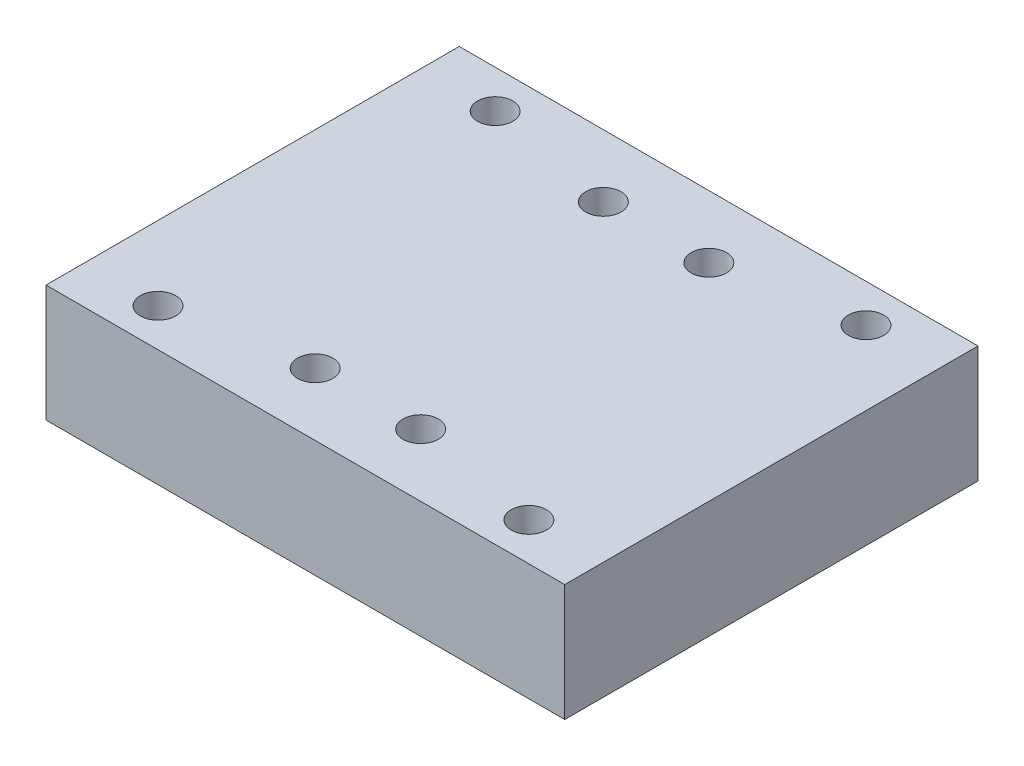
SolidWorks part; units mm, degrees
ref_plane "Front Plane" through (0, 0, 0) normal (0, 0, 1) x (1, 0, 0)
ref_plane "Top Plane" through (0, 0, 0) normal (0, 1, 0) x (1, 0, 0)
ref_plane "Right Plane" through (0, 0, 0) normal (1, 0, 0) x (0, 0, -1)
sketch "Sketch1" plane through (0, 0, 0) normal (0, 1, 0) x (1, 0, 0)
  line L1 (-47.7, -38) -> (47.7, -38)
  line L2 (-47.7, -38) -> (-47.7, 38)
  line L3 (-47.7, 38) -> (47.7, 38)
  line L4 (47.7, -38) -> (47.7, 38)
  line L5 (-47.7, -38) -> (47.7, 38) construction
  line L6 (-47.7, 38) -> (47.7, -38) construction
  point P0 (0, 0)
  dimension "D1" = 76
  dimension "D2" = 95.4
extrude "Boss-Extrude1" add sketch "Sketch1" along normal blind 21.5
sketch "Sketch2" plane through (0, 21.5, 0) normal (0, 1, 0) x (1, 0, 0)
  line L0 (47.7, 38) -> (-47.7, 38) construction
  line L1 (-47.7, 38) -> (-47.7, -38) construction
  circle A0 centre (-34.1, 31) radius 3.25
  circle A2 centre (-9.7, 26.5) radius 3.25
  dimension "D1" = 6.5
  dimension "D2" = 7
  dimension "D3" = 13.6
  dimension "D4" = 38
  dimension "D5" = 11.5
extrude "Cut-Extrude1" cut sketch "Sketch2" against normal through all
mirror "Mirror1" about plane through (0, 0, 0) normal (1, 0, 0) of "Cut-Extrude1" second plane through (0, 0, 0) second plane normal (0, 0, 1)
